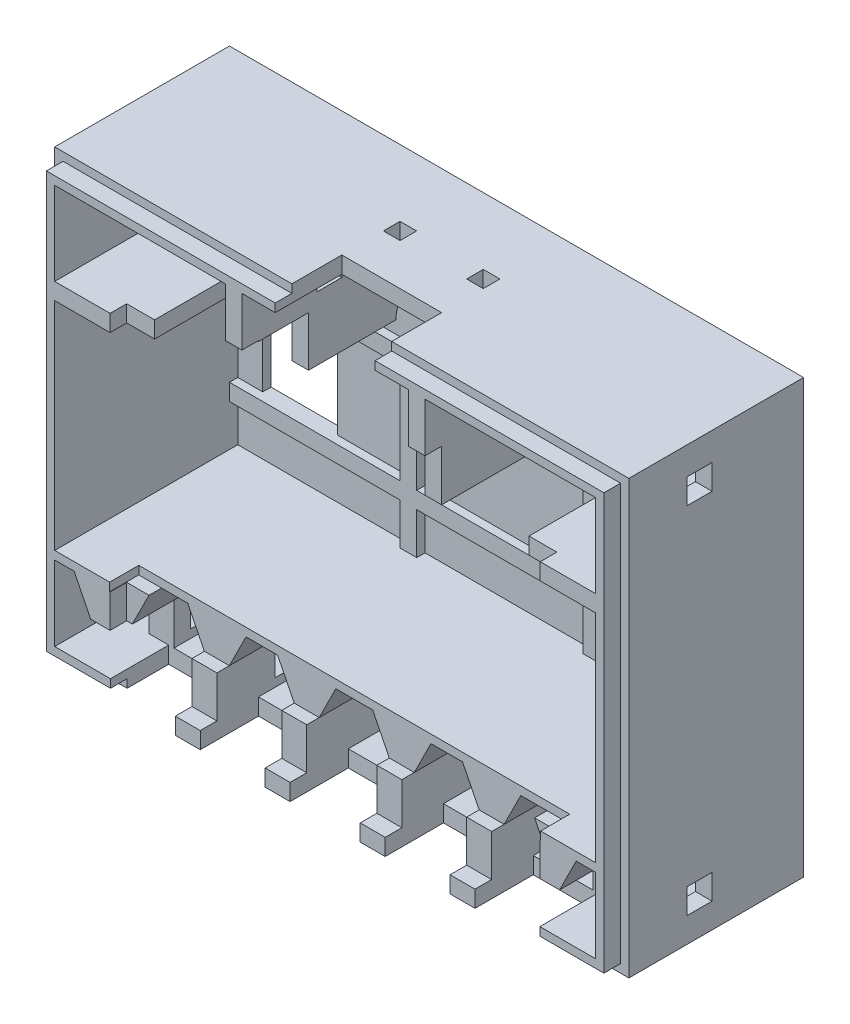
SolidWorks part; units mm, degrees
ref_plane "Přední rovina" through (0, 0, 0) normal (0, 0, 1) x (1, 0, 0)
ref_plane "Horní rovina" through (0, 0, 0) normal (0, 1, 0) x (1, 0, 0)
ref_plane "Pravá rovina" through (0, 0, 0) normal (1, 0, 0) x (0, 0, -1)
sketch "Skica1" plane through (0, 0, 0) normal (0, 0, 1) x (1, 0, 0)
  line L1 (-32.5, -24) -> (32.5, -24)
  line L2 (-32.5, -24) -> (-32.5, 24)
  line L3 (-32.5, 24) -> (32.5, 24)
  line L4 (32.5, -24) -> (32.5, 24)
  line L5 (-32.5, -24) -> (32.5, 24) construction
  line L6 (-32.5, 24) -> (32.5, -24) construction
  point P0 (0, 0)
  dimension "D1" = 65
  dimension "D2" = 48
extrude "Vysunout tenkostěnný1" add sketch "Skica1" along normal blind 23 thin
sketch "Skica2" plane through (0, 0, 0) normal (0, 0, 1) x (1, 0, 0)
  line L0 (0, -1000) -> (0, 49000) construction
  line L1 (-1000, -15) -> (49000, -15) construction
  line L2 (-32.5, -24) -> (32.5, -24) construction
  line L3 (-32.5, 24) -> (-32.5, -24) construction
  line L4 (-32.5, -15) -> (32.5, -15) construction
  line L5 (-32.5, -15) -> (-32.5, -14)
  line L6 (-32.5, -14) -> (32.5, -14)
  line L7 (32.5, -15) -> (32.5, -14)
  line L8 (32.5, -24) -> (32.5, 24) construction
  line L9 (-1000, 12) -> (49000, 12) construction
  line L10 (-5.715, -15) -> (-5.715, -24) construction
  line L11 (32.5, 24) -> (-32.5, 24) construction
  line L12 (-32.5, 12) -> (-22.5, 12)
  line L13 (-32.5, 12) -> (-32.5, 14)
  line L14 (-32.5, 14) -> (-22.5, 14)
  line L15 (-22.5, 12) -> (-22.5, 14)
  line L16 (22.5, 12) -> (22.5, 14)
  line L17 (32.5, 12) -> (22.5, 12)
  line L18 (32.5, 14) -> (22.5, 14)
  line L19 (32.5, 12) -> (32.5, 14)
  line L20 (12, 12) -> (10, 12)
  line L21 (-12, 24) -> (-10, 24)
  line L22 (-12, 24) -> (-12, 12)
  line L23 (-12, 12) -> (-10, 12)
  line L24 (-10, 24) -> (-10, 12)
  line L25 (10, 24) -> (10, 12)
  line L26 (12, 24) -> (10, 24)
  line L27 (12, 24) -> (12, 12)
  line L28 (-1009.0572, -19) -> (48990.9428, -19) construction
  line L29 (-11.43, -2.7573) -> (-11.43, 7.2902) construction
  line L30 (-7.215, -15) -> (-4.215, -15) construction
  line L31 (-7.215, -15) -> (-7.215, -24) construction
  line L32 (-7.215, -24) -> (-4.215, -24)
  line L33 (-4.215, -15) -> (-4.215, -24) construction
  line L34 (-21.59, -1004.6629) -> (-21.59, 48995.3371) construction
  line L35 (-4.215, -19) -> (-2.215, -15)
  line L36 (-7.215, -19) -> (-9.215, -15)
  line L37 (-7.215, -19) -> (-7.215, -24)
  line L38 (-4.215, -24) -> (-4.215, -19)
  line L39 (-16.51, -15) -> (-16.51, -24) construction
  line L40 (-26.67, -15) -> (-26.67, -24) construction
  line L41 (-20.01, -15) -> (-18.01, -19)
  line L42 (-18.01, -19) -> (-18.01, -24)
  line L43 (-18.01, -24) -> (-15.01, -24)
  line L44 (-15.01, -24) -> (-15.01, -19)
  line L45 (-15.01, -19) -> (-13.01, -15)
  line L46 (-30.17, -15) -> (-28.17, -19)
  line L47 (-28.17, -19) -> (-28.17, -24)
  line L48 (-28.17, -24) -> (-25.17, -24)
  line L49 (-25.17, -24) -> (-25.17, -19)
  line L50 (-25.17, -19) -> (-23.17, -15)
  line L51 (-32.5, -15) -> (-30.17, -15)
  line L52 (-23.17, -15) -> (-20.01, -15)
  line L53 (-13.01, -15) -> (-9.215, -15)
  line L54 (-2.215, -15) -> (2.215, -15)
  line L55 (4.215, -19) -> (2.215, -15)
  line L56 (4.215, -24) -> (4.215, -19)
  line L57 (7.215, -24) -> (4.215, -24)
  line L58 (7.215, -19) -> (7.215, -24)
  line L59 (7.215, -19) -> (9.215, -15)
  line L60 (13.01, -15) -> (9.215, -15)
  line L61 (15.01, -19) -> (13.01, -15)
  line L62 (15.01, -24) -> (15.01, -19)
  line L63 (18.01, -24) -> (15.01, -24)
  line L64 (18.01, -19) -> (18.01, -24)
  line L65 (20.01, -15) -> (18.01, -19)
  line L66 (23.17, -15) -> (20.01, -15)
  line L67 (25.17, -19) -> (23.17, -15)
  line L68 (25.17, -24) -> (25.17, -19)
  line L69 (28.17, -24) -> (25.17, -24)
  line L70 (28.17, -19) -> (28.17, -24)
  line L71 (30.17, -15) -> (28.17, -19)
  line L72 (32.5, -15) -> (30.17, -15)
  point P69 (0, -15)
  dimension "D1" = 9
  dimension "D2" = 1
  dimension "D3" = 26
  dimension "D4" = 10
  dimension "D5" = 36
  dimension "D6" = 2
  dimension "D7" = 10
  dimension "D8" = 10
  dimension "D9" = 2
  dimension "D10" = 21.59
  dimension "D11" = 3
  dimension "D12" = 11.43
  dimension "D13" = 4
  dimension "D14" = 7
extrude "Přidat žebra" add sketch "Skica2" along normal up to surface (23 mm away) up to face at (0, 0, 23)
sketch "Skica3" plane through (0, 0, 23) normal (0, 0, 1) x (1, 0, 0)
  line L0 (-10, 12) -> (-10, 24) construction
  line L1 (-12, 12) -> (-10, 12)
  line L2 (-12, 12) -> (-12, 18)
  line L3 (-12, 18) -> (-10, 18)
  line L4 (-10, 12) -> (-10, 18)
  line L5 (-12, 24) -> (-32.5, 24) construction
  line L6 (0, -1000) -> (0, 49000) construction
  line L7 (10, 24) -> (-10, 24) construction
  line L8 (-6, 24) -> (6, 24)
  line L9 (-6, 24) -> (-6, 26)
  line L10 (-6, 26) -> (6, 26)
  line L11 (6, 24) -> (6, 26)
  line L12 (34.5, 26) -> (-34.5, 26) construction
  dimension "D1" = 6
  dimension "D2" = 12
extrude "Odebrat 8 mm" cut sketch "Skica3" against normal blind 8
sketch "Skica4" plane through (0, 0, 23) normal (0, 0, 1) x (1, 0, 0)
  line L0 (-34.5, -26) -> (34.5, -26) construction
  line L1 (-4.215, -24) -> (4.215, -24)
  line L2 (-4.215, -24) -> (-4.215, -26)
  line L3 (-4.215, -26) -> (4.215, -26)
  line L4 (4.215, -24) -> (4.215, -26)
  line L5 (4.215, -19) -> (4.215, -24) construction
  line L6 (-7.215, -19) -> (-7.215, -24) construction
  line L7 (7.215, -24) -> (15.01, -24)
  line L8 (7.215, -24) -> (7.215, -26)
  line L9 (7.215, -26) -> (15.01, -26)
  line L10 (15.01, -24) -> (15.01, -26)
  line L11 (-15.01, -24) -> (-7.215, -24)
  line L12 (-15.01, -24) -> (-15.01, -26)
  line L13 (-15.01, -26) -> (-7.215, -26)
  line L14 (-7.215, -24) -> (-7.215, -26)
  line L16 (18.01, -24) -> (18.01, -26)
  line L17 (18.01, -26) -> (25.8, -26)
  line L18 (25.8, -24) -> (25.8, -26)
  line L20 (-18.01, -24) -> (-18.01, -26)
  line L21 (-18.01, -26) -> (-25.8, -26)
  line L22 (-25.8, -24) -> (-25.8, -26)
  line L23 (15.01, -19) -> (15.01, -24) construction
  line L24 (0, -1000) -> (0, 49000) construction
  line L25 (-28.17, -24) -> (-25.8, -24)
  line L26 (-28.17, -24) -> (-25.17, -24) construction
  line L27 (-28.17, -24) -> (-28.17, -19)
  line L28 (-28.17, -19) -> (-25.17, -19)
  line L29 (-25.17, -24) -> (-25.17, -19)
  line L30 (25.17, -24) -> (28.17, -24) construction
  line L31 (25.17, -24) -> (25.17, -19)
  line L32 (25.17, -19) -> (28.17, -19)
  line L33 (28.17, -24) -> (28.17, -19)
  line L34 (25.8, -24) -> (28.17, -24)
  line L35 (-25.17, -24) -> (-18.01, -24)
  line L36 (18.01, -24) -> (25.17, -24)
  dimension "D1" = 51.6
extrude "Odebrat 7 mm" cut sketch "Skica4" against normal blind 7
sketch "Skica5" plane through (0, 0, 23) normal (0, 0, 1) x (1, 0, 0)
  line L0 (0, -1000) -> (0, 49000) construction
  line L1 (32.5, -14) -> (-32.5, -14) construction
  line L2 (-25.9, -13) -> (25.9, -13)
  line L3 (-25.9, -13) -> (-25.9, -15)
  line L4 (-25.9, -15) -> (25.9, -15) construction
  line L5 (25.9, -13) -> (25.9, -15)
  line L6 (-25.9, -13) -> (25.9, -15) construction
  line L7 (-25.9, -15) -> (25.9, -13) construction
  line L8 (-2.215, -15) -> (2.215, -15) construction
  line L9 (-25.9, -15) -> (-20.01, -15)
  line L10 (-20.01, -15) -> (20.01, -15) construction
  line L11 (-20.01, -15) -> (-20.01, -19)
  line L12 (-20.01, -19) -> (20.01, -19)
  line L13 (20.01, -15) -> (20.01, -19)
  line L14 (20.01, -15) -> (25.9, -15)
  point P1 (0, -14)
  dimension "D1" = 51.8
extrude "Odebrat 3,5 mm" cut sketch "Skica5" against normal blind 3.5
sketch "Skica6" plane through (0, 0, 23) normal (0, 0, 1) x (1, 0, 0)
  line L0 (0, -1000) -> (0, 49000) construction
  line L2 (-25.85, -24) -> (25.85, -24)
  line L3 (-25.85, -24) -> (-25.85, 18.1)
  line L4 (-25.85, 18.1) -> (25.85, 18.1)
  line L5 (25.85, -24) -> (25.85, 18.1)
  line L7 (-32.5, -24) -> (-25.8, -24) construction
  line L8 (-1000, 0) -> (49000, 0) construction
  line L9 (-34.5, 26) -> (34.5, 26)
  line L10 (-34.5, 26) -> (-34.5, -26)
  line L11 (-34.5, -26) -> (34.5, -26) construction
  line L12 (34.5, 26) -> (34.5, -26)
  line L13 (-33.5, 25) -> (33.5, 25)
  line L14 (-33.5, 25) -> (-33.5, -25)
  line L15 (-33.5, -25) -> (33.5, -25) construction
  line L16 (33.5, 25) -> (33.5, -25)
  line L17 (-34.5, -26) -> (-25.8, -26)
  line L18 (-25.8, -26) -> (-25.8, -25)
  line L20 (-25.8, -25) -> (-33.5, -25)
  line L21 (33.5, -25) -> (25.8, -25)
  line L24 (25.8, -25) -> (25.8, -26)
  line L25 (25.8, -26) -> (34.5, -26)
  line L26 (25.8, -26) -> (25.8, -24) construction
  line L27 (-25.8, -24) -> (-25.8, -26) construction
  dimension "D1" = 51.7
  dimension "D2" = 42.1
  dimension "D3" = 1
  dimension "D4" = 1
extrude "Odebrat 2 mm" cut sketch "Skica6" against normal blind 2
sketch "Skica8" plane through (0, 0, 0) normal (0, 0, 1) x (1, 0, 0)
  line L0 (-34.5, -26) -> (34.5, -26) construction
  line L1 (-34.5, 26) -> (-34.5, -26) construction
  line L2 (34.5, -26) -> (34.5, 26) construction
  line L3 (34.5, 26) -> (-34.5, 26) construction
  line L4 (-34.5, -26) -> (34.5, -26)
  line L5 (-34.5, 26) -> (-34.5, -26)
  line L6 (34.5, -26) -> (34.5, 26)
  line L7 (34.5, 26) -> (-34.5, 26)
extrude "Přidat dno" add sketch "Skica8" along normal blind 1
sketch "Skica9" plane through (0, 0, 0) normal (0, 0, 1) x (1, 0, 0)
  line L0 (32.5, -14) -> (-32.5, -14) construction
  line L1 (-12, 7) -> (-10, 7)
  line L2 (-12, 7) -> (-12, -14)
  line L3 (-12, -14) -> (-10, -14)
  line L4 (-10, 7) -> (-10, -14)
  line L5 (-10, 12) -> (-10, 24) construction
  line L6 (10, 7) -> (12, 7)
  line L7 (10, 7) -> (10, -14)
  line L8 (10, -14) -> (12, -14)
  line L9 (12, 7) -> (12, -14)
  line L10 (12, 12) -> (12, 24) construction
  line L11 (-32.5, 12) -> (-32.5, -14) construction
  line L12 (-32.5, 7) -> (32.5, 7)
  line L13 (-32.5, 7) -> (-32.5, 5)
  line L14 (-32.5, 5) -> (32.5, 5)
  line L15 (32.5, 7) -> (32.5, 5)
  line L16 (32.5, -14) -> (32.5, 12) construction
  line L17 (-32.5, 12) -> (-32.5, -14) construction
  line L18 (-32.5, -7) -> (32.5, -7)
  line L19 (-32.5, -7) -> (-32.5, -9)
  line L20 (-32.5, -9) -> (32.5, -9)
  line L21 (32.5, -7) -> (32.5, -9)
  line L22 (32.5, -14) -> (32.5, 12) construction
  line L23 (-32.5, 12) -> (-22.5, 12) construction
  line L25 (-12, 24) -> (-12, 12) construction
  line L26 (10, 24) -> (10, 12) construction
  dimension "D1" = 2
  dimension "D2" = 2
  dimension "D3" = 5
  dimension "D4" = 5
extrude "Přidat žebra (dno)" add sketch "Skica9" along normal blind 2 contours L13 L14 L2 L12 | L2 L12 L4 L1 | L7 L12 L9 L6 | L2 L14 L4 L12 | L4 L14 L7 L12 | L7 L14 L9 L12 | L15 L12 L9 L14 | L7 L18 L9 L14 | L2 L18 L4 L14 | L19 L20 L2 L18 | L20 L2 L3 L4 | L2 L20 L4 L18 | L4 L20 L7 L18 | L7 L20 L9 L18 | L20 L7 L8 L9 | L21 L18 L9 L20
sketch "Skica10" plane through (0, 0, 0) normal (0, 0, -1) x (-1, 0, 0)
  line L0 (12, 5) -> (32.5, 5) construction
  line L1 (20.5, 5) -> (29.5, 5)
  line L2 (20.5, 5) -> (20.5, -7)
  line L3 (20.5, -7) -> (29.5, -7)
  line L4 (29.5, 5) -> (29.5, -7)
  line L5 (12, -7) -> (32.5, -7) construction
  line L8 (34.5, 26) -> (34.5, -26) construction
  dimension "D1" = 5
  dimension "D2" = 9
extrude "Odebrat vypínač" cut sketch "Skica10" against normal through all
ref_plane "Rovina1" through (4.25, -4.25, 0) normal (-0.7071, 0.7071, 0) x (0.7071, 0.7071, 0)
sketch "Skica11" plane through (4.25, -4.25, 0) normal (-0.7071, 0.7071, 0) x (0.7071, 0.7071, 0)
  line L0 (25.8094, -1) -> (25.8094, -11)
  line L1 (25.8094, -21) -> (25.8094, -1) construction
  line L2 (25.8094, -11) -> (33.8094, -11)
  line L3 (33.8094, -11) -> (33.8094, -9)
  line L4 (32.8805, -1) -> (25.8094, -1) construction
  line L5 (25.8094, -1) -> (24.3952, -1) construction
  line L6 (25.8094, -1) -> (27.8094, -1)
  line L7 (27.8094, -1) -> (27.8094, -3)
  arc A0 (27.8094, -3) -> (33.8094, -9) centre (33.8094, -3) ccw
  dimension "D1" = 2
  dimension "D2" = 8
  dimension "D3" = 2
extrude "Přidat háček" add sketch "Skica11" against normal blind 2
sketch "Skica12" plane through (34.5, 0, 0) normal (1, 0, 0) x (0, 0, -1)
  line L0 (-12.5, -1030.8385) -> (-12.5, 48969.1615) construction
  line L1 (-11, 18.2426) -> (-11, 19.6569) construction
  line L2 (-11, 19.6569) -> (-14, 19.6569)
  line L3 (-11, 19.6569) -> (-11, 22.6569)
  line L4 (-11, 22.6569) -> (-14, 22.6569)
  line L5 (-14, 19.6569) -> (-14, 22.6569)
  line L6 (-11, 19.6569) -> (-14, 22.6569) construction
  line L7 (-11, 22.6569) -> (-14, 19.6569) construction
  line L8 (-11, -23) -> (-14, -23)
  line L9 (-11, -23) -> (-11, -20)
  line L10 (-11, -20) -> (-14, -20)
  line L11 (-14, -23) -> (-14, -20)
  line L12 (-11, -23) -> (-14, -20) construction
  line L13 (-11, -20) -> (-14, -23) construction
  line L14 (-11, 19.6569) -> (-9, 19.6569) construction
  line L17 (-1012.5, -21.5) -> (48987.5, -21.5) construction
  line L18 (-16, -19) -> (-1, -19) construction
  line L19 (-16, -24) -> (-1, -24) construction
  line L20 (-16, -24) -> (-1, -24) construction
  line L21 (-16, -19) -> (-1, -19) construction
  point P1 (-12.5, 21.1569)
  point P7 (-12.5, -21.5)
  dimension "D1" = 3
extrude "Odebrat vysunutím1" cut sketch "Skica12" against normal up to surface (24.5 mm away) up to face at (10, 18.0333, 15)
sketch "Skica13" plane through (-34.5, 0, 0) normal (-1, 0, 0) x (0, 0, 1)
  line L0 (11, 22.6569) -> (14, 22.6569) construction
  line L1 (14, 19.6569) -> (11, 19.6569) construction
  line L2 (11, 19.6569) -> (11, 22.6569) construction
  line L3 (14, 22.6569) -> (14, 19.6569) construction
  line L4 (11, -20) -> (14, -20) construction
  line L5 (11, -23) -> (11, -20) construction
  line L6 (14, -20) -> (14, -23) construction
  line L7 (14, -23) -> (11, -23) construction
  line L8 (14, 19.6569) -> (11, 19.6569)
  line L9 (11, 19.6569) -> (11, 22.6569)
  line L10 (14, 22.6569) -> (14, 19.6569)
  line L11 (11, 22.6569) -> (14, 22.6569)
  line L12 (11, -20) -> (14, -20)
  line L13 (11, -23) -> (11, -20)
  line L14 (14, -20) -> (14, -23)
  line L15 (14, -23) -> (11, -23)
extrude "Odebrat vysunutím2" cut sketch "Skica13" against normal up to surface (24.5 mm away) up to face at (-10, 18.025, 15)
sketch "Skica14" plane through (0, 26, 0) normal (0, 1, 0) x (1, 0, 0)
  line L0 (0, -1000) -> (0, 49000) construction
  line L1 (6, -15) -> (6, -21) construction
  line L2 (4, -8) -> (6, -8)
  line L3 (4, -8) -> (4, -10)
  line L4 (4, -10) -> (6, -10)
  line L5 (6, -8) -> (6, -10)
  line L6 (4, -8) -> (6, -10) construction
  line L7 (4, -10) -> (6, -8) construction
  line L10 (6, -15) -> (-6, -15) construction
  line L11 (-4, -8) -> (-4, -10)
  line L12 (-4, -8) -> (-6, -8)
  line L13 (-6, -8) -> (-6, -10)
  line L14 (-4, -10) -> (-6, -10)
  point P1 (5, -9)
  dimension "D1" = 2
  dimension "D2" = 5
extrude "Odebrat vysunutím3" cut sketch "Skica14" against normal up to next
sketch "Skica15" plane through (12, 0, 0) normal (1, 0, 0) x (0, 0, -1)
  line L0 (-21, 12) -> (-1, 12) construction
  line L1 (-1, 12) -> (-1, 24) construction
  line L3 (-1, 15.5) -> (-1, 12)
  line L4 (-1, 12) -> (-4.5, 12)
  arc A0 (-4.5, 12) -> (-1, 15.5) centre (-1, 12) cw
  dimension "D1" = 3.5
extrude "Odebrat vysunutím4" cut sketch "Skica15" against normal up to surface (24 mm away) up to face at (-12, 21.1569, 12.5)
